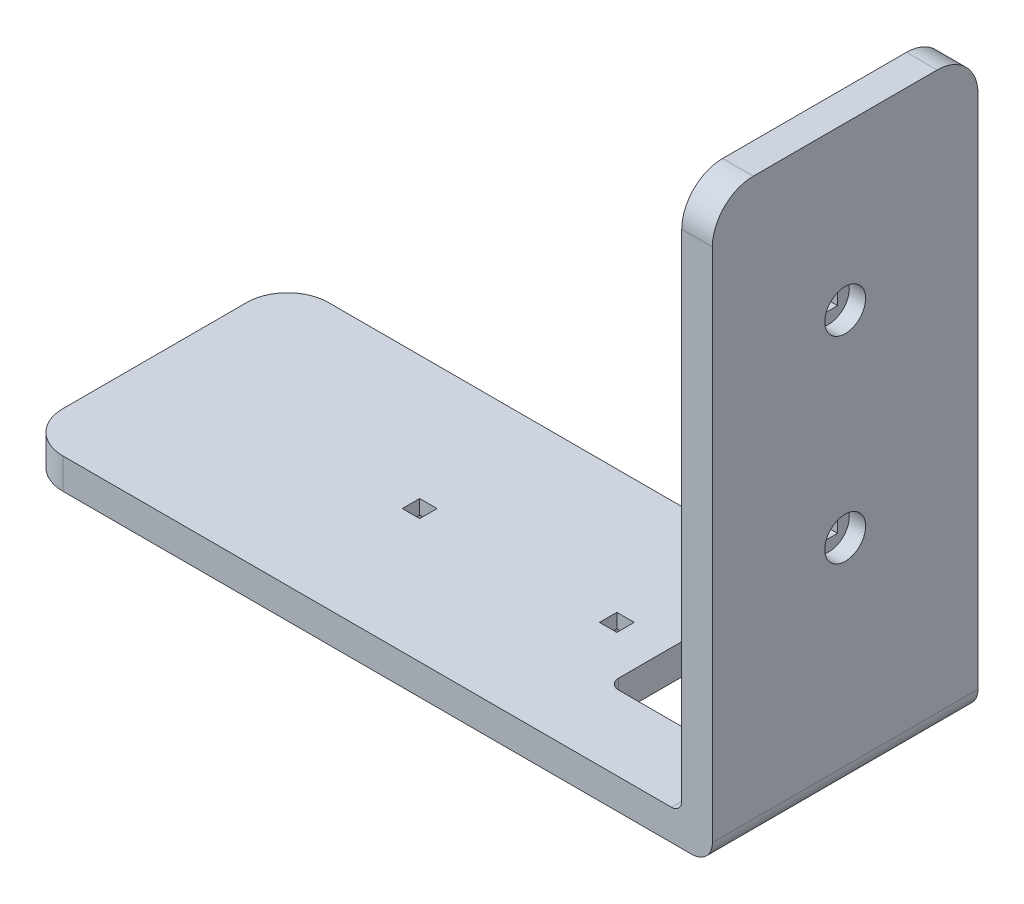
SolidWorks part; units mm, degrees
ref_plane "Спереди" through (0, 0, 0) normal (0, 0, 1) x (1, 0, 0)
ref_plane "Сверху" through (0, 0, 0) normal (0, 1, 0) x (1, 0, 0)
ref_plane "Справа" through (0, 0, 0) normal (1, 0, 0) x (0, 0, -1)
sketch "Эскиз1" plane through (0, 0, 0) normal (0, 1, 0) x (1, 0, 0)
  line L1 (-27.0825, 18.0349) -> (36.4975, 18.0349)
  line L2 (-31.0825, 14.0349) -> (-31.0825, -3.9651)
  line L3 (-27.0825, -7.9651) -> (36.4975, -7.9651)
  line L4 (36.4975, 18.0349) -> (36.4975, -7.9651)
  arc A0 (-31.0825, -3.9651) -> (-27.0825, -7.9651) centre (-27.0825, -3.9651) ccw
  arc A1 (-27.0825, 18.0349) -> (-31.0825, 14.0349) centre (-27.0825, 14.0349) ccw
  dimension "D2" = 4
  dimension "D1" = 26
  dimension "D3" = 67.58
extrude "Бобышка-Вытянуть1" add sketch "Эскиз1" along normal blind 3
sketch "Эскиз2" plane through (0, 3, 0) normal (0, 1, 0) x (1, 0, 0)
  line L0 (-27.0825, -7.9651) -> (36.4975, -7.9651) construction
  line L1 (36.4975, 18.0349) -> (33.4975, 18.0349)
  line L2 (36.4975, 18.0349) -> (36.4975, -7.9651)
  line L3 (36.4975, -7.9651) -> (33.4975, -7.9651)
  line L4 (33.4975, 18.0349) -> (33.4975, -7.9651)
  dimension "D1" = 3
extrude "Бобышка-Вытянуть2" add sketch "Эскиз2" along normal blind 53.5
fillet "Скругление1" radius 4 2 edges at (34.9975, 56.5, -18.0349) (34.9975, 56.5, 7.9651)
fillet "Скругление2" radius 2 1 edges at (36.4975, 0, -5.0349)
fillet "Скругление3" radius 1 1 edges at (33.4975, 3, -5.0349)
sketch "Эскиз3" plane through (0, 0, 0) normal (0, -1, 0) x (1, 0, 0)
  line L0 (13.2975, -5.8849) -> (14.9975, -5.8849) construction
  line L1 (-6.0025, -4.1849) -> (-4.3025, -4.1849)
  line L2 (-6.0025, -4.1849) -> (-6.0025, -5.8849)
  line L3 (-6.0025, -5.8849) -> (-4.3025, -5.8849)
  line L4 (-4.3025, -4.1849) -> (-4.3025, -5.8849)
  line L5 (13.2975, -4.1849) -> (14.9975, -4.1849)
  line L6 (13.2975, -4.1849) -> (13.2975, -5.8849)
  line L7 (13.2975, -5.8849) -> (14.9975, -5.8849)
  line L8 (14.9975, -4.1849) -> (14.9975, -5.8849)
  line L9 (13.2975, -4.1849) -> (13.2975, -5.8849) construction
  line L10 (-6.0025, -5.8849) -> (-4.3025, -5.8849) construction
  line L11 (-6.0025, -4.1849) -> (-6.0025, -5.8849) construction
  dimension "D1" = 1.7
  dimension "D2" = 1.7
  dimension "D3" = 1.7
  dimension "D4" = 1.7
  dimension "D5" = 0
  dimension "D6" = 0
  dimension "D7" = 0
  dimension "D8" = 0
extrude "Вырез-Вытянуть1" cut sketch "Эскиз3" against normal blind 3
sketch "Эскиз4" plane through (0, 0, 0) normal (0, -1, 0) x (1, 0, 0)
  circle A0 centre (-5.1525, -5.0349) radius 2
  circle A1 centre (14.1475, -5.0349) radius 2
  dimension "D1" = 4
  dimension "D2" = 4
extrude "Вырез-Вытянуть2" cut sketch "Эскиз4" against normal blind 1.6
sketch "Эскиз5" plane through (36.4975, 0, 0) normal (1, 0, 0) x (0, 0, -1)
  line L0 (4.1849, 22.2) -> (4.1849, 20.5) construction
  line L1 (5.8849, 20.5) -> (4.1849, 20.5)
  line L2 (5.8849, 20.5) -> (5.8849, 22.2)
  line L3 (5.8849, 22.2) -> (4.1849, 22.2)
  line L4 (4.1849, 20.5) -> (4.1849, 22.2)
  line L5 (5.8849, 39.8) -> (4.1849, 39.8)
  line L6 (5.8849, 39.8) -> (5.8849, 41.5)
  line L7 (5.8849, 41.5) -> (4.1849, 41.5)
  line L8 (4.1849, 39.8) -> (4.1849, 41.5)
  line L9 (5.8849, 22.2) -> (4.1849, 22.2) construction
  line L10 (5.8849, 41.5) -> (4.1849, 41.5) construction
  line L11 (4.1849, 41.5) -> (4.1849, 39.8) construction
  point P8 (4.1849, 40.65)
  point P9 (5.0349, 41.5)
  point P10 (5.8849, 21.35)
  dimension "D1" = 1.7
  dimension "D2" = 1.7
  dimension "D3" = 1.7
  dimension "D4" = 1.7
  dimension "D5" = 0
  dimension "D6" = 0
  dimension "D7" = 0
  dimension "D8" = 0
extrude "Вырез-Вытянуть3" cut sketch "Эскиз5" against normal blind 3
sketch "Эскиз6" plane through (36.4975, 0, 0) normal (1, 0, 0) x (0, 0, -1)
  circle A0 centre (5.0349, 40.65) radius 2
  circle A1 centre (5.0349, 21.35) radius 2
  dimension "D1" = 4
  dimension "D2" = 4
extrude "Вырез-Вытянуть4" cut sketch "Эскиз6" against normal blind 1.6
sketch "Эскиз7" plane through (0, 0, 0) normal (0, -1, 0) x (1, 0, 0)
  line L0 (20.7475, -10.6849) -> (26.0475, -10.6849) construction
  line L1 (19.9575, 0.6151) -> (26.2575, 0.6151)
  line L2 (18.9575, -0.3849) -> (18.9575, -9.6849)
  line L3 (19.9575, -10.6849) -> (26.2575, -10.6849)
  line L4 (27.2575, -0.3849) -> (27.2575, -9.6849)
  line L5 (26.0475, 0.6151) -> (20.7475, 0.6151) construction
  line L6 (33.4975, -18.0349) -> (33.4975, 7.9651) construction
  arc A0 (19.9575, 0.6151) -> (18.9575, -0.3849) centre (19.9575, -0.3849) ccw
  arc A1 (26.2575, 0.6151) -> (27.2575, -0.3849) centre (26.2575, -0.3849) cw
  arc A2 (26.2575, -10.6849) -> (27.2575, -9.6849) centre (26.2575, -9.6849) ccw
  arc A3 (18.9575, -9.6849) -> (19.9575, -10.6849) centre (19.9575, -9.6849) ccw
  dimension "D4" = 1
  dimension "D1" = 0
  dimension "D2" = 0
  dimension "D3" = 8.3
  dimension "D5" = 6.24
extrude "Вырез-Вытянуть5" cut sketch "Эскиз7" against normal blind 3
